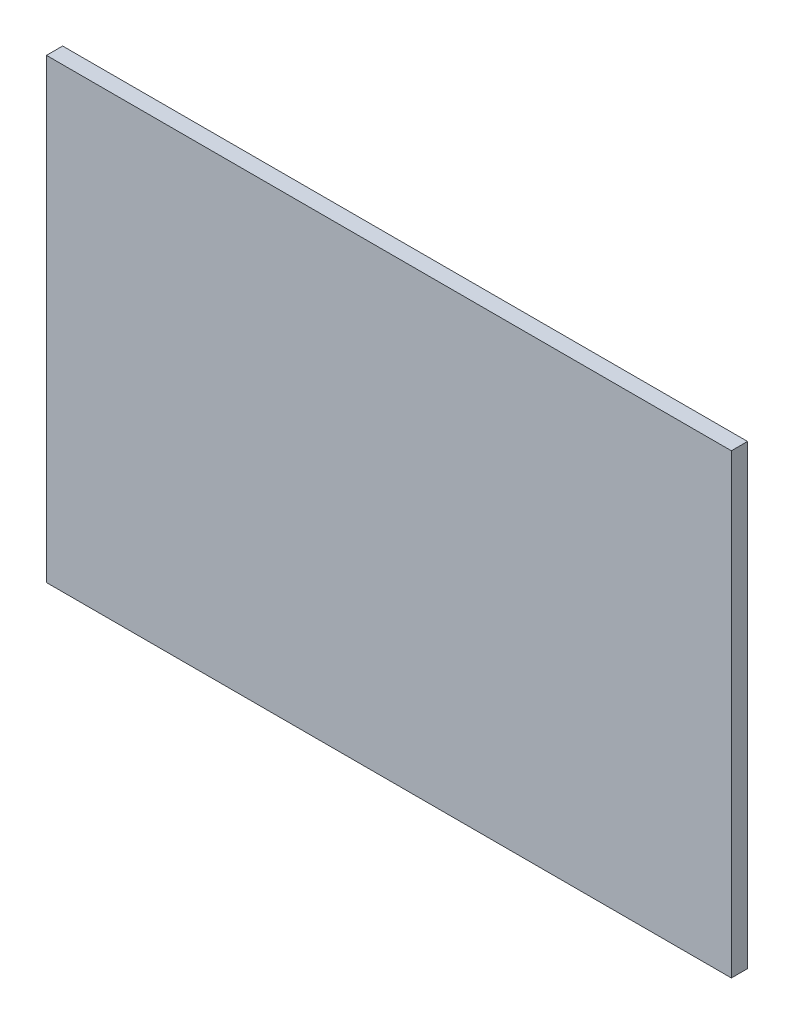
SolidWorks part; units mm, degrees
ref_plane "Front Plane" through (0, 0, 0) normal (0, 0, 1) x (1, 0, 0)
ref_plane "Top Plane" through (0, 0, 0) normal (0, 1, 0) x (1, 0, 0)
ref_plane "Right Plane" through (0, 0, 0) normal (1, 0, 0) x (0, 0, -1)
sketch "Sketch1" plane through (0, 0, 0) normal (0, 0, 1) x (1, 0, 0)
  line L1 (40.26, -26.84) -> (-40.26, -26.84)
  line L2 (40.26, -26.84) -> (40.26, 26.84)
  line L3 (40.26, 26.84) -> (-40.26, 26.84)
  line L4 (-40.26, -26.84) -> (-40.26, 26.84)
  line L5 (40.26, -26.84) -> (-40.26, 26.84) construction
  line L6 (40.26, 26.84) -> (-40.26, -26.84) construction
  point P0 (0, 0)
  dimension "D1" = 53.68
  dimension "D2" = 80.52
extrude "Boss-Extrude1" add sketch "Sketch1" along normal blind 1.9
